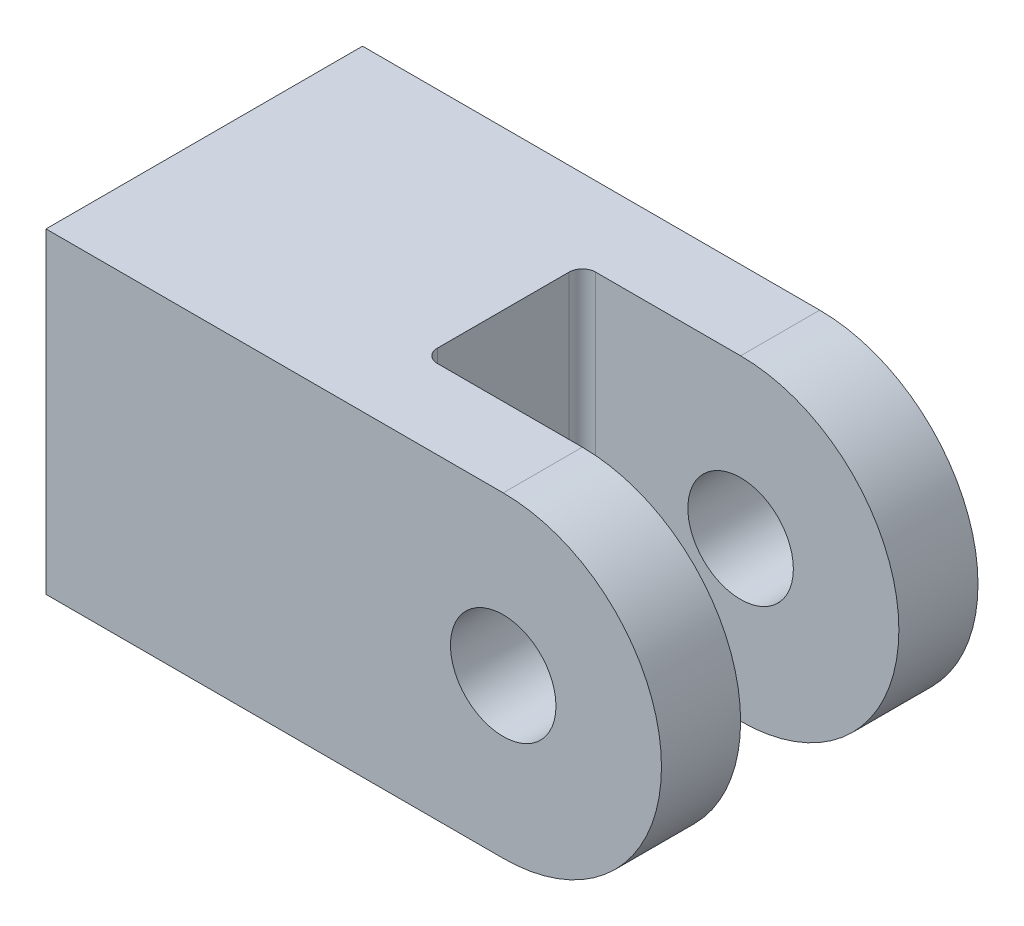
SolidWorks part; units mm, degrees
ref_plane "Front Plane" through (0, 0, 0) normal (0, 0, 1) x (1, 0, 0)
ref_plane "Top Plane" through (0, 0, 0) normal (0, 1, 0) x (1, 0, 0)
ref_plane "Right Plane" through (0, 0, 0) normal (1, 0, 0) x (0, 0, -1)
sketch "Sketch1" plane through (0, 0, 0) normal (0, 0, 1) x (1, 0, 0)
  line L0 (0, 0) -> (52, 0)
  line L1 (0, 0) -> (0, 36)
  line L2 (0, 36) -> (52, 36)
  line L4 (52, 0) -> (52, 0.3881)
  arc A0 (52, 0) -> (52, 36) centre (52, 18) ccw
  dimension "D1" = 36
  dimension "D2" = 52
extrude "Clevis Body Extrude1" add sketch "Sketch1" along normal mid plane 36 contours L0 L1 L2 A0
sketch "Sketch2" plane through (0, 0, 0) normal (0, 0, 1) x (1, 0, 0)
  line L0 (0, 0) -> (0, 36) construction
  line L1 (0, 0) -> (52, 0) construction
  circle A0 centre (52, 18) radius 6
  dimension "D2" = 18
  dimension "D3" = 12
  dimension "D1" = 52
extrude "Pin Holes Cut-Extrude1" cut sketch "Sketch2" against normal mid plane 36
sketch "Sketch3" plane through (0, 0, 0) normal (-1, 0, 0) x (0, 0, 1)
  line L0 (18, 12) -> (18, 24) construction
  line L1 (18, 0) -> (-18, 0) construction
  circle A0 centre (0, 18) radius 7.5
  dimension "D3" = 15
  dimension "D1" = 18
  dimension "D2" = 18
extrude "Threaded Hole Cut-Extrude2" cut sketch "Sketch3" against normal blind 25
cosmetic thread "Cosmetic Thread4" parameters "D2"=16
sketch "Sketch5" plane through (0, 0, 0) normal (0, 1, 0) x (1, 0, 0)
  line L0 (0, -18) -> (52, -18) construction
  line L1 (34, -9) -> (72, -9)
  line L2 (34, -9) -> (34, 9)
  line L3 (34, 9) -> (72, 9)
  line L4 (72, -9) -> (72, 9)
  dimension "D1" = 18
  dimension "D2" = 34
  dimension "D3" = 9
  dimension "D4" = 38
extrude "Clevis Gap Cut-Extrude4" cut sketch "Sketch5" along normal through all
fillet "Fillet2" radius 1.5 2 edges at (34, 18, -9) (34, 18, 9)
chamfer "Chamfer2" distance 0.5 angle 45 1 edges at (0, 18, 7.5)
